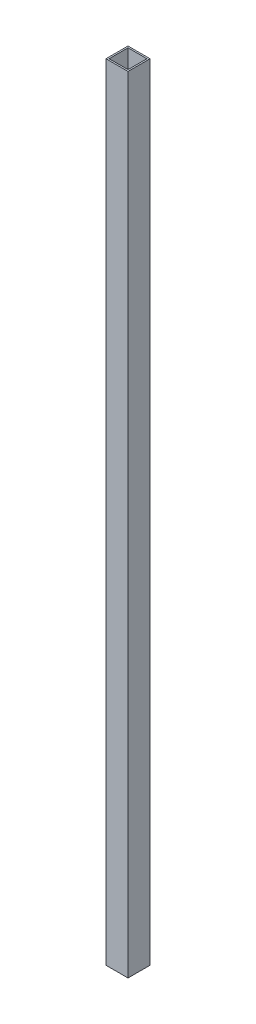
SolidWorks part; units mm, degrees
material "6061 Alloy"
ref_plane "Front Plane" through (0, 0, 0) normal (0, 0, 1) x (1, 0, 0)
ref_plane "Top Plane" through (0, 0, 0) normal (0, 1, 0) x (1, 0, 0)
ref_plane "Right Plane" through (0, 0, 0) normal (1, 0, 0) x (0, 0, -1)
sketch "Sketch1" plane through (0, 0, 0) normal (0, 1, 0) x (1, 0, 0)
  line L1 (-8.5, 8.5) -> (8.5, 8.5)
  line L2 (-8.5, 8.5) -> (-8.5, -8.5)
  line L3 (-8.5, -8.5) -> (8.5, -8.5)
  line L4 (8.5, 8.5) -> (8.5, -8.5)
  line L5 (-8.5, 8.5) -> (8.5, -8.5) construction
  line L6 (-8.5, -8.5) -> (8.5, 8.5) construction
  line L7 (-7.3, 7.3) -> (7.3, 7.3)
  line L8 (-7.3, 7.3) -> (-7.3, -7.3)
  line L9 (-7.3, -7.3) -> (7.3, -7.3)
  line L10 (7.3, 7.3) -> (7.3, -7.3)
  line L11 (-7.3, 7.3) -> (7.3, -7.3) construction
  line L12 (-7.3, -7.3) -> (7.3, 7.3) construction
  point P0 (0, 0)
  point P6 (0, 0)
  dimension "D1" = 14.6
  dimension "D2" = 17
extrude "Boss-Extrude1" add sketch "Sketch1" along normal blind 606 contours L1 L4 L3 L2 | L9 L10 L7 L8
